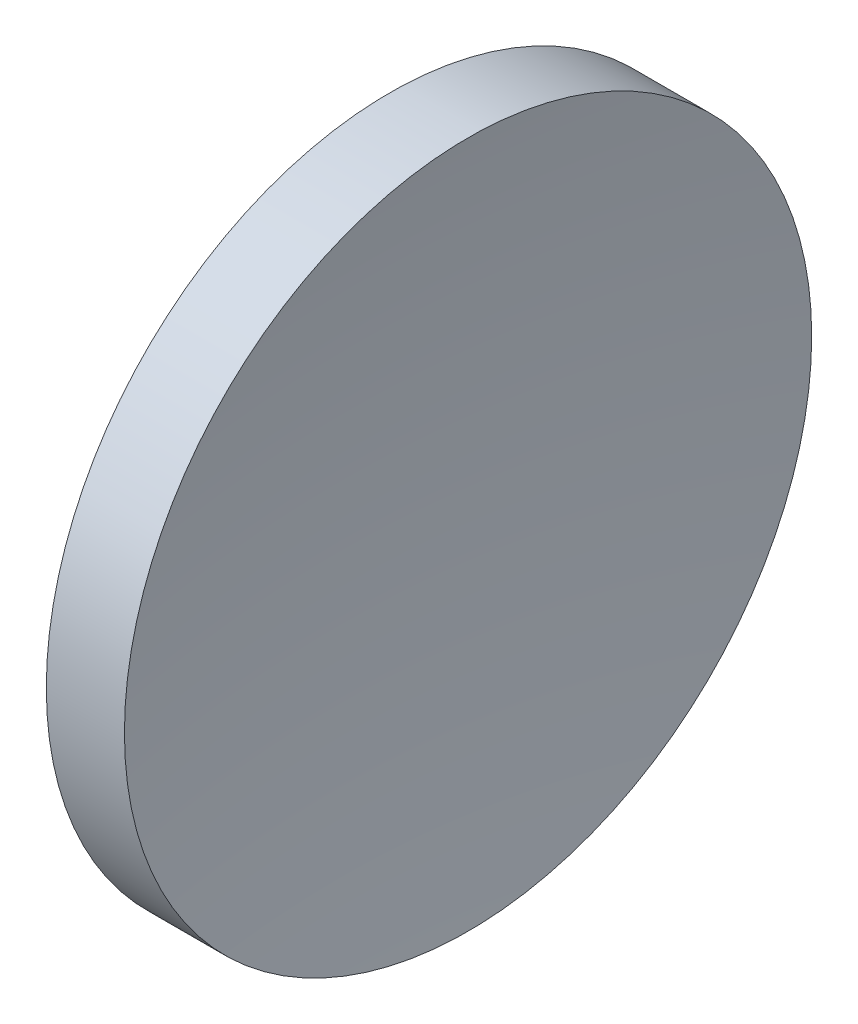
SolidWorks part; units mm, degrees
ref_plane "前视基准面" through (0, 0, 0) normal (0, 0, 1) x (1, 0, 0)
ref_plane "上视基准面" through (0, 0, 0) normal (0, 1, 0) x (1, 0, 0)
ref_plane "右视基准面" through (0, 0, 0) normal (1, 0, 0) x (0, 0, -1)
sketch "草图1" plane through (0, 0, 0) normal (0, 0, 1) x (1, 0, 0)
  line L0 (111.9552, 71.194) -> (132.4701, 71.194) construction
  line L1 (119.3629, 71.194) -> (119.3629, 83.894)
  line L2 (119.3629, 83.894) -> (122.2501, 83.894)
  line L3 (121.3629, 71.194) -> (119.3629, 71.194)
  arc A0 (122.2501, 83.894) -> (121.3629, 71.194) centre (213.0629, 71.1692) ccw
revolve "旋转1" add sketch "草图1" angle 360 about L0
